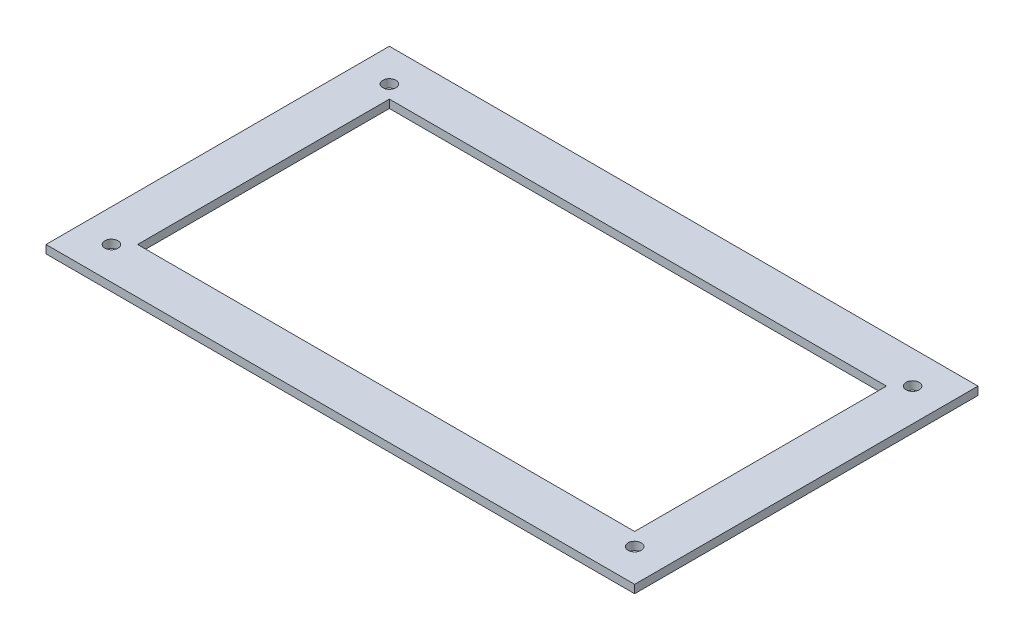
SolidWorks part; units mm, degrees
material "AISI 1020"
ref_plane "Front Plane" through (0, 0, 0) normal (0, 0, 1) x (1, 0, 0)
ref_plane "Top Plane" through (0, 0, 0) normal (0, 1, 0) x (1, 0, 0)
ref_plane "Right Plane" through (0, 0, 0) normal (1, 0, 0) x (0, 0, -1)
sketch "Sketch1" plane through (0, 0, 0) normal (0, 1, 0) x (1, 0, 0)
  line L1 (-180, -105) -> (180, -105)
  line L2 (-180, -105) -> (-180, 105)
  line L3 (-180, 105) -> (180, 105)
  line L4 (180, -105) -> (180, 105)
  line L5 (-180, -105) -> (180, 105) construction
  line L6 (-180, 105) -> (180, -105) construction
  line L7 (-152, -77) -> (152, -77)
  line L8 (-152, -77) -> (-152, 77)
  line L9 (-152, 77) -> (152, 77)
  line L10 (152, -77) -> (152, 77)
  line L11 (-152, -77) -> (152, 77) construction
  line L12 (-152, 77) -> (152, -77) construction
  point P0 (0, 0)
  point P6 (0, 0)
  dimension "D1" = 360
  dimension "D2" = 210
  dimension "D3" = 304
  dimension "D4" = 154
  dimension "D5" = 28
  dimension "D6" = 28
extrude "Boss-Extrude1" add sketch "Sketch1" along normal blind 5
sketch "Sketch2" plane through (0, 5, 0) normal (0, 1, 0) x (1, 0, 0)
  line L0 (-180, -105) -> (180, -105) construction
  line L1 (-180, 105) -> (-180, -105) construction
  circle A0 centre (-160, -85) radius 4
  circle A1 centre (160, -85) radius 4
  circle A2 centre (160, 85) radius 4
  circle A3 centre (-160, 85) radius 4
  dimension "D1" = 20
  dimension "D2" = 20
  dimension "D3" = 2
  dimension "D4" = 2
extrude "Cut-Extrude1" cut sketch "Sketch2" against normal blind 10
